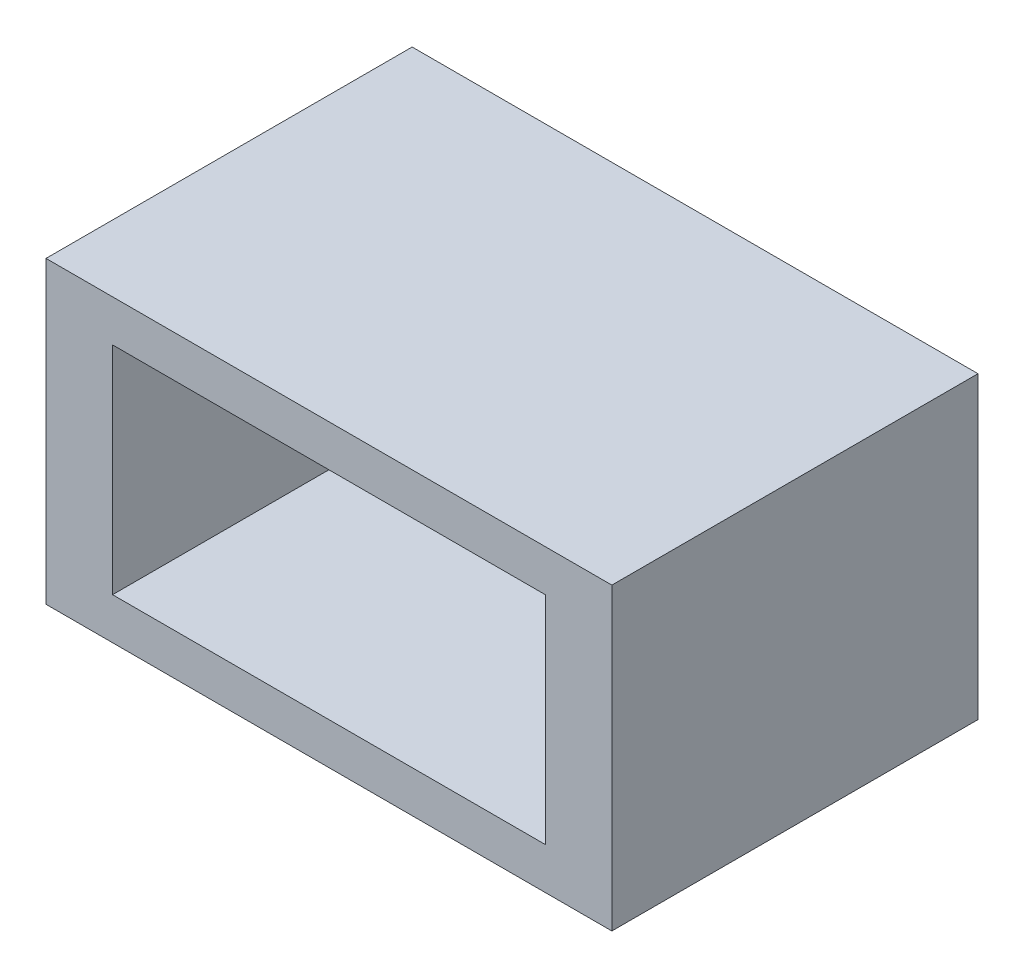
SolidWorks part; units mm, degrees
ref_plane "Plan de face" through (0, 0, 0) normal (0, 0, 1) x (1, 0, 0)
ref_plane "Plan de dessus" through (0, 0, 0) normal (0, 1, 0) x (1, 0, 0)
ref_plane "Plan de droite" through (0, 0, 0) normal (1, 0, 0) x (0, 0, -1)
sketch "Esquisse1" plane through (0, 0, 0) normal (0, 0, 1) x (1, 0, 0)
  line L1 (-8.5, 4.5) -> (8.5, 4.5)
  line L2 (-8.5, 4.5) -> (-8.5, -4.5)
  line L3 (-8.5, -4.5) -> (8.5, -4.5)
  line L4 (8.5, 4.5) -> (8.5, -4.5)
  line L5 (-8.5, 4.5) -> (8.5, -4.5) construction
  line L6 (-8.5, -4.5) -> (8.5, 4.5) construction
  point P0 (0, 0)
  dimension "D1" = 17
  dimension "D2" = 9
extrude "Boss.-Extru.1" add sketch "Esquisse1" along normal blind 11
sketch "Esquisse2" plane through (0, 0, 11) normal (0, 0, 1) x (1, 0, 0)
  line L1 (-6.5, 3.25) -> (6.5, 3.25)
  line L2 (-6.5, 3.25) -> (-6.5, -3.25)
  line L3 (-6.5, -3.25) -> (6.5, -3.25)
  line L4 (6.5, 3.25) -> (6.5, -3.25)
  line L5 (-6.5, 3.25) -> (6.5, -3.25) construction
  line L6 (-6.5, -3.25) -> (6.5, 3.25) construction
  point P0 (0, 0)
  dimension "D1" = 13
  dimension "D2" = 6.5
extrude "Enlèv. mat.-Extru.1" cut sketch "Esquisse2" against normal up to surface (11 mm away) contours L1 L4 L3 L2 up to face at (0, 0, 0)
